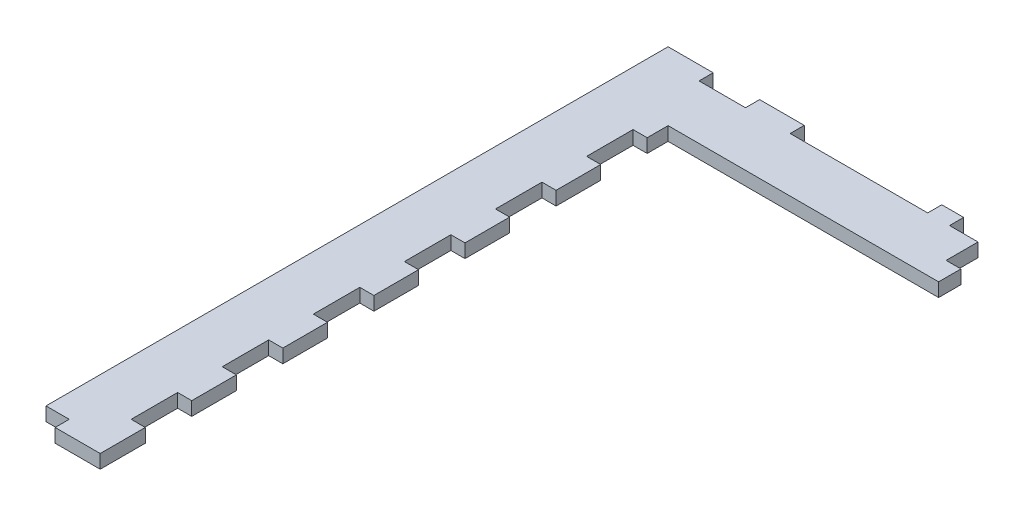
SolidWorks part; units mm, degrees
ref_plane "Front Plane" through (0, 0, 0) normal (0, 0, 1) x (1, 0, 0)
ref_plane "Top Plane" through (0, 0, 0) normal (0, 1, 0) x (1, 0, 0)
ref_plane "Right Plane" through (0, 0, 0) normal (1, 0, 0) x (0, 0, -1)
sketch "Sketch1" plane through (0, 0, 0) normal (0, 1, 0) x (1, 0, 0)
  line L0 (0, -139.6944) -> (15, -139.6944) construction
  line L1 (0, 0) -> (75, 0)
  line L2 (0, 0) -> (0, -139.6944)
  line L3 (0, -139.6944) -> (15, -139.6944)
  line L4 (15, -15) -> (15, -139.6944)
  line L5 (15, -15) -> (75, -15)
  line L6 (75, -15) -> (75, 0)
extrude "Boss-Extrude1" add sketch "Sketch1" against normal up to vertex (3 mm away)
sketch "Sketch2" plane through (0, 0, 0) normal (0, 1, 0) x (1, 0, 0)
  line L0 (12, -79.6944) -> (15, -79.6944) construction
  line L1 (12, -79.6944) -> (15, -79.6944)
  line L2 (12, -79.6944) -> (12, -89.6944)
  line L3 (12, -89.6944) -> (15, -89.6944)
  line L4 (40, -3) -> (40, 0)
  line L5 (30, -3) -> (40, -3)
  line L6 (30, 0) -> (30, -3)
  line L7 (40, 0) -> (30, 0)
  line L8 (71.25, -3) -> (65, -3)
  line L9 (30, -3) -> (60, -3)
  line L10 (30, 0) -> (30, -3)
  line L11 (60, 0) -> (30, 0)
  line L12 (20, 0) -> (10, 0)
  line L13 (10, 0) -> (10, -3)
  line L14 (10, -3) -> (20, -3)
  line L15 (20, -3) -> (20, 0)
  line L16 (20, 0) -> (10, 0)
  line L17 (10, 0) -> (10, -3)
  line L18 (10, -3) -> (20, -3)
  line L19 (20, -3) -> (20, 0)
  line L20 (60, -3) -> (60, 0)
  line L21 (50, -3) -> (60, -3)
  line L22 (50, 0) -> (50, -3)
  line L23 (60, 0) -> (50, 0)
  line L24 (60, -3) -> (60, 0)
  line L25 (65, -3) -> (65, 0)
  line L27 (65, 0) -> (75, 0)
  line L28 (5, -139.6944) -> (5, -136.6944)
  line L29 (0, -139.6944) -> (5, -139.6944)
  line L30 (0, -136.6944) -> (0, -139.6944)
  line L31 (5, -136.6944) -> (0, -136.6944)
  line L32 (5, -139.6944) -> (5, -136.6944)
  line L33 (0, -139.6944) -> (5, -139.6944)
  line L34 (0, -136.6944) -> (0, -139.6944)
  line L35 (5, -136.6944) -> (0, -136.6944)
  line L36 (15, -129.6944) -> (15, -119.6944)
  line L37 (12, -129.6944) -> (15, -129.6944)
  line L38 (12, -119.6944) -> (12, -129.6944)
  line L39 (15, -119.6944) -> (12, -119.6944)
  line L40 (15, -129.6944) -> (15, -119.6944)
  line L41 (12, -129.6944) -> (15, -129.6944)
  line L42 (12, -119.6944) -> (12, -129.6944)
  line L43 (15, -119.6944) -> (12, -119.6944)
  line L44 (12, -69.6944) -> (15, -69.6944)
  line L45 (15, -69.6944) -> (15, -59.6944)
  line L46 (15, -59.6944) -> (12, -59.6944)
  line L47 (12, -59.6944) -> (12, -69.6944)
  line L48 (12, -69.6944) -> (15, -69.6944)
  line L49 (15, -69.6944) -> (15, -59.6944)
  line L50 (15, -59.6944) -> (12, -59.6944)
  line L51 (12, -59.6944) -> (12, -69.6944)
  line L52 (12, -109.6944) -> (15, -109.6944)
  line L53 (15, -109.6944) -> (15, -99.6944)
  line L54 (15, -99.6944) -> (12, -99.6944)
  line L55 (12, -99.6944) -> (12, -109.6944)
  line L56 (12, -109.6944) -> (15, -109.6944)
  line L57 (15, -109.6944) -> (15, -99.6944)
  line L58 (15, -99.6944) -> (12, -99.6944)
  line L59 (12, -99.6944) -> (12, -109.6944)
  line L60 (15, -79.6944) -> (15, -89.6944)
  line L61 (15, -89.6944) -> (12, -89.6944) construction
  line L62 (12, 0) -> (12, -136.6944) construction
  line L63 (15, -86.7444) -> (15, -139.6944) construction
  line L68 (12, -29.6944) -> (15, -29.6944)
  line L69 (12, -19.6944) -> (12, -29.6944)
  line L70 (15, -19.6944) -> (12, -19.6944)
  line L71 (15, -29.6944) -> (15, -19.6944)
  line L72 (12, -29.6944) -> (15, -29.6944)
  line L73 (12, -19.6944) -> (12, -29.6944)
  line L74 (15, -19.6944) -> (12, -19.6944)
  line L75 (15, -29.6944) -> (15, -19.6944)
  line L76 (12, -39.6944) -> (12, -49.6944)
  line L77 (12, -49.6944) -> (15, -49.6944)
  line L78 (15, -49.6944) -> (15, -39.6944)
  line L79 (15, -39.6944) -> (12, -39.6944)
  line L80 (12, -39.6944) -> (12, -49.6944)
  line L81 (12, -49.6944) -> (15, -49.6944)
  line L82 (15, -49.6944) -> (15, -39.6944)
  line L83 (15, -39.6944) -> (12, -39.6944)
  line L100 (71.25, -3) -> (71.25, -10)
  line L101 (71.25, -10) -> (74.5, -10)
  line L102 (74.5, -10) -> (74.5, -15)
  line L103 (74.5, -15) -> (75, -15)
  line L104 (75, -15) -> (75, 0)
  line L105 (75, 0) -> (70, 0)
  line L106 (70, 0) -> (70, -3)
  line L107 (70, -3) -> (71.25, -3)
  line L108 (71.25, -3) -> (71.25, -10)
  line L109 (71.25, -10) -> (74.5, -10)
  line L110 (74.5, -10) -> (74.5, -15)
  line L111 (74.5, -15) -> (75, -15)
  line L112 (75, -15) -> (75, 0)
  line L113 (75, 0) -> (70, 0) construction
  line L114 (70, 0) -> (70, -3) construction
  line L115 (70, -3) -> (71.25, -3) construction
  dimension "D1" = 0
  dimension "D2" = 0
  dimension "D3" = 0
  dimension "D4" = 0
  dimension "D5" = 0
  dimension "D6" = 0
  dimension "D7" = 0
  dimension "D9" = 0
  dimension "D10" = 0
  dimension "D12" = 0
sketch "Sketch3" plane through (0, 0, 0) normal (0, 1, 0) x (1, 0, 0)
  line L0 (5.1, -139.7944) -> (5.1, -136.5944)
  line L1 (5.1, -136.5944) -> (-0.1, -136.5944)
  line L2 (-0.1, -136.5944) -> (-0.1, -139.7944)
  line L3 (-0.1, -139.7944) -> (5.1, -139.7944)
  line L4 (5, -139.6944) -> (5, -136.6944)
  line L5 (5, -136.6944) -> (0, -136.6944)
  line L6 (0, -136.6944) -> (0, -139.6944)
  line L7 (0, -139.6944) -> (5, -139.6944)
  line L8 (5, -139.6944) -> (5, -136.6944) construction
  line L9 (5, -136.6944) -> (0, -136.6944) construction
  line L10 (0, -136.6944) -> (0, -139.6944) construction
  line L11 (0, -139.6944) -> (5, -139.6944) construction
  line L12 (20, 0) -> (10, 0)
  line L13 (10, 0) -> (10, -3)
  line L14 (10, -3) -> (20, -3)
  line L15 (20, -3) -> (20, 0)
  line L16 (20, 0) -> (10, 0) construction
  line L17 (10, 0) -> (10, -3) construction
  line L18 (10, -3) -> (20, -3) construction
  line L19 (20, -3) -> (20, 0) construction
  line L20 (30, -3) -> (60, -3)
  line L21 (60, -3) -> (60, 0)
  line L22 (60, 0) -> (30, 0)
  line L23 (30, 0) -> (30, -3)
  line L24 (30, -3) -> (60, -3) construction
  line L25 (60, -3) -> (60, 0) construction
  line L26 (60, 0) -> (30, 0) construction
  line L27 (30, 0) -> (30, -3) construction
  line L28 (12, -109.6944) -> (15, -109.6944)
  line L29 (15, -109.6944) -> (15, -99.6944)
  line L30 (15, -99.6944) -> (12, -99.6944)
  line L31 (12, -99.6944) -> (12, -109.6944)
  line L32 (12, -109.6944) -> (15, -109.6944) construction
  line L33 (15, -109.6944) -> (15, -99.6944) construction
  line L34 (15, -99.6944) -> (12, -99.6944) construction
  line L35 (12, -99.6944) -> (12, -109.6944) construction
  line L36 (12, -69.6944) -> (15, -69.6944)
  line L37 (15, -69.6944) -> (15, -59.6944)
  line L38 (15, -59.6944) -> (12, -59.6944)
  line L39 (12, -59.6944) -> (12, -69.6944)
  line L40 (12, -69.6944) -> (15, -69.6944) construction
  line L41 (15, -69.6944) -> (15, -59.6944) construction
  line L42 (15, -59.6944) -> (12, -59.6944) construction
  line L43 (12, -59.6944) -> (12, -69.6944) construction
  line L44 (15, -129.6944) -> (15, -119.6944)
  line L45 (15, -119.6944) -> (12, -119.6944)
  line L46 (12, -119.6944) -> (12, -129.6944)
  line L47 (12, -129.6944) -> (15, -129.6944)
  line L48 (15, -129.6944) -> (15, -119.6944) construction
  line L49 (15, -119.6944) -> (12, -119.6944) construction
  line L50 (12, -119.6944) -> (12, -129.6944) construction
  line L51 (12, -129.6944) -> (15, -129.6944) construction
  line L52 (12, -39.6944) -> (12, -49.6944)
  line L53 (12, -49.6944) -> (15, -49.6944)
  line L54 (15, -49.6944) -> (15, -39.6944)
  line L55 (15, -39.6944) -> (12, -39.6944)
  line L56 (12, -39.6944) -> (12, -49.6944) construction
  line L57 (12, -49.6944) -> (15, -49.6944) construction
  line L58 (15, -49.6944) -> (15, -39.6944) construction
  line L59 (15, -39.6944) -> (12, -39.6944) construction
  line L60 (12, -19.6944) -> (12, -29.6944)
  line L61 (15, -19.6944) -> (12, -19.6944)
  line L62 (15, -29.6944) -> (15, -19.6944)
  line L63 (12, -29.6944) -> (15, -29.6944)
  line L64 (12, -19.6944) -> (12, -29.6944) construction
  line L65 (15, -19.6944) -> (12, -19.6944) construction
  line L66 (15, -29.6944) -> (15, -19.6944) construction
  line L67 (12, -29.6944) -> (15, -29.6944) construction
  line L68 (15, -79.6944) -> (12, -79.6944)
  line L69 (12, -79.6944) -> (12, -89.6944)
  line L70 (12, -89.6944) -> (15, -89.6944)
  line L71 (15, -89.6944) -> (15, -79.6944)
  line L72 (15, -79.6944) -> (12, -79.6944) construction
  line L73 (12, -79.6944) -> (12, -89.6944) construction
  line L74 (12, -89.6944) -> (15, -89.6944) construction
  line L75 (15, -89.6944) -> (15, -79.6944) construction
  line L76 (20.1, 0.1) -> (9.9, 0.1)
  line L77 (9.9, 0.1) -> (9.9, -3.1)
  line L78 (9.9, -3.1) -> (20.1, -3.1)
  line L79 (20.1, -3.1) -> (20.1, 0.1)
  line L80 (75, 0) -> (65, 0)
  line L81 (65, 0) -> (65, -3)
  line L82 (65, -3) -> (71.25, -3)
  line L83 (71.25, -3) -> (71.25, -10)
  line L84 (71.25, -10) -> (74.5, -10)
  line L85 (74.5, -10) -> (74.5, -15)
  line L86 (74.5, -15) -> (75, -15)
  line L87 (75, -15) -> (75, 0)
  line L88 (75, 0) -> (65, 0) construction
  line L89 (65, 0) -> (65, -3) construction
  line L90 (65, -3) -> (71.25, -3) construction
  line L91 (71.25, -3) -> (71.25, -10) construction
  line L92 (71.25, -10) -> (74.5, -10) construction
  line L93 (74.5, -10) -> (74.5, -15) construction
  line L94 (74.5, -15) -> (75, -15) construction
  line L95 (75, -15) -> (75, 0) construction
  line L96 (29.9, -3.1) -> (60.1, -3.1)
  line L97 (60.1, -3.1) -> (60.1, 0.1)
  line L98 (60.1, 0.1) -> (29.9, 0.1)
  line L99 (29.9, 0.1) -> (29.9, -3.1)
  line L100 (11.9, -109.7944) -> (15.1, -109.7944)
  line L101 (15.1, -109.7944) -> (15.1, -99.5944)
  line L102 (15.1, -99.5944) -> (11.9, -99.5944)
  line L103 (11.9, -99.5944) -> (11.9, -109.7944)
  line L104 (11.9, -69.7944) -> (15.1, -69.7944)
  line L105 (15.1, -69.7944) -> (15.1, -59.5944)
  line L106 (15.1, -59.5944) -> (11.9, -59.5944)
  line L107 (11.9, -59.5944) -> (11.9, -69.7944)
  line L108 (15.1, -129.7944) -> (15.1, -119.5944)
  line L109 (15.1, -119.5944) -> (11.9, -119.5944)
  line L110 (11.9, -119.5944) -> (11.9, -129.7944)
  line L111 (11.9, -129.7944) -> (15.1, -129.7944)
  line L112 (11.9, -39.5944) -> (11.9, -49.7944)
  line L113 (11.9, -49.7944) -> (15.1, -49.7944)
  line L114 (15.1, -49.7944) -> (15.1, -39.5944)
  line L115 (15.1, -39.5944) -> (11.9, -39.5944)
  line L116 (11.9, -19.5944) -> (11.9, -29.7944)
  line L117 (11.9, -29.7944) -> (15.1, -29.7944)
  line L118 (15.1, -29.7944) -> (15.1, -19.5944)
  line L119 (15.1, -19.5944) -> (11.9, -19.5944)
  line L120 (15.1, -79.5944) -> (11.9, -79.5944)
  line L121 (11.9, -79.5944) -> (11.9, -89.7944)
  line L122 (11.9, -89.7944) -> (15.1, -89.7944)
  line L123 (15.1, -89.7944) -> (15.1, -79.5944)
  line L124 (75.1, 0.1) -> (64.9, 0.1)
  line L125 (64.9, 0.1) -> (64.9, -3.1)
  line L126 (64.9, -3.1) -> (71.15, -3.1)
  line L127 (71.15, -3.1) -> (71.15, -10.1)
  line L128 (71.15, -10.1) -> (74.4, -10.1)
  line L129 (74.4, -10.1) -> (74.4, -15.1)
  line L130 (74.4, -15.1) -> (75.1, -15.1)
  line L131 (75.1, -15.1) -> (75.1, 0.1)
  dimension "D1" = 0
  dimension "D2" = 0
  dimension "D3" = 0
  dimension "D4" = 0
  dimension "D5" = 0
  dimension "D6" = 0
  dimension "D7" = 0
  dimension "D8" = 0
  dimension "D9" = 0
  dimension "D10" = 0
  dimension "D11" = 0.1
extrude "Cut-Extrude1" cut sketch "Sketch3" against normal through all
